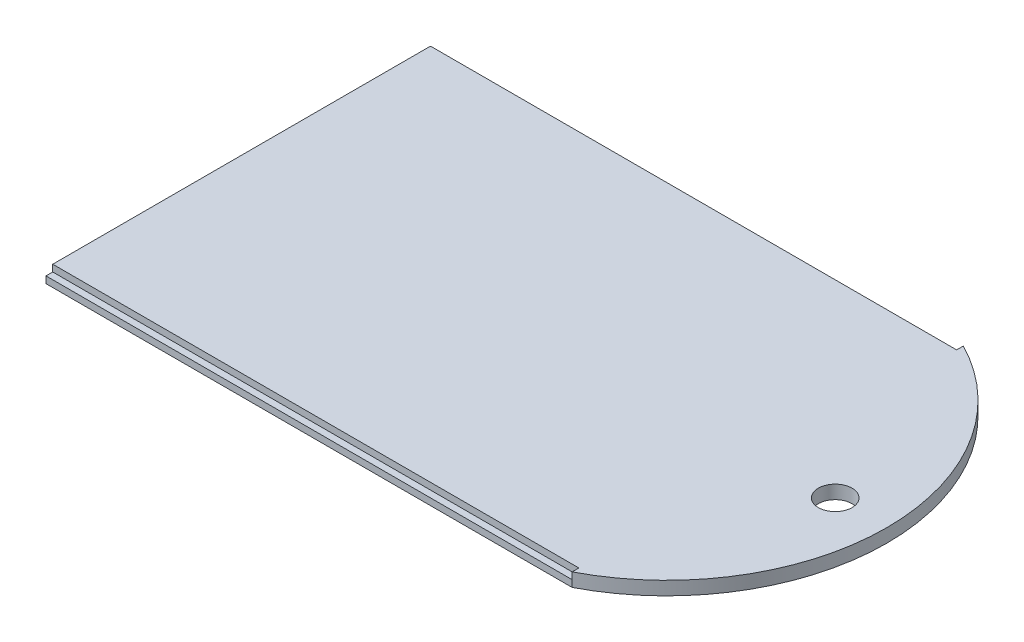
SolidWorks part; units mm, degrees
ref_plane "Ebene vorne" through (0, 0, 0) normal (0, 0, 1) x (1, 0, 0)
ref_plane "Ebene oben" through (0, 0, 0) normal (0, 1, 0) x (1, 0, 0)
ref_plane "Ebene rechts" through (0, 0, 0) normal (1, 0, 0) x (0, 0, -1)
sketch "Skizze1" plane through (0, 0, 0) normal (0, 1, 0) x (1, 0, 0)
  line L1 (0, 0) -> (78, 0)
  line L2 (0, 0) -> (0, 58)
  line L3 (0, 58) -> (78, 58)
  arc A0 (78, 58) -> (78, 0) centre (63, 29) cw
  circle A1 centre (88, 29) radius 2.5
  dimension "D5" = 5
  dimension "D1" = 78
  dimension "D2" = 58
  dimension "D3" = 63
  dimension "D4" = 78
  dimension "D6" = 25
extrude "Aufsatz-Linear austragen1" add sketch "Skizze1" along normal blind 2
sketch "Skizze2" plane through (0, 2, 0) normal (0, 1, 0) x (1, 0, 0)
  line L1 (0, 58) -> (78, 58)
  line L2 (0, 58) -> (0, 57)
  line L3 (0, 57) -> (78, 57)
  line L4 (78, 58) -> (78, 57)
  line L5 (0, 0) -> (78, 0)
  line L6 (0, 0) -> (0, 1)
  line L7 (0, 1) -> (78, 1)
  line L8 (78, 0) -> (78, 1)
  dimension "D1" = 78
  dimension "D2" = 1
  dimension "D3" = 1
  dimension "D4" = 78
extrude "Schnitt-Linear austragen1" cut sketch "Skizze2" against normal blind 1
